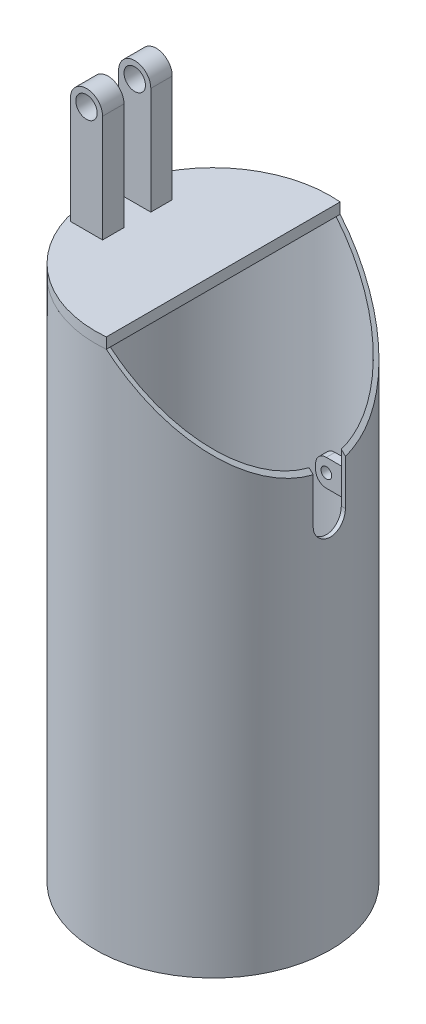
SolidWorks part; units mm, degrees
ref_plane "Plano frontal" through (0, 0, 0) normal (0, 0, 1) x (1, 0, 0)
ref_plane "Plano superior" through (0, 0, 0) normal (0, 1, 0) x (1, 0, 0)
ref_plane "Plano direito" through (0, 0, 0) normal (1, 0, 0) x (0, 0, -1)
sketch "Esboço1" plane through (0, 0, 0) normal (0, 0, 1) x (1, 0, 0)
  line L0 (0, 0) -> (0, 490) construction
  line L1 (0, 0) -> (215.8131, 0) construction
  line L2 (105.78, 490) -> (109.54, 490)
  line L4 (105.78, 0) -> (109.54, 0)
  line L7 (105.78, 0) -> (105.78, 490)
  line L11 (109.54, 490) -> (109.54, 0)
  dimension "D1" = 3.76
  dimension "D6" = 490
  dimension "D7" = 219.08
revolve "Revolução1" add sketch "Esboço1" angle 360 about L0
sketch "Esboço2" plane through (0, 0, 0) normal (0, 0, 1) x (1, 0, 0)
  line L0 (9.54, 490) -> (109.54, 390)
  line L1 (109.54, 490) -> (-109.54, 490) construction
  line L2 (109.54, 0) -> (109.54, 490) construction
  line L3 (109.54, 390) -> (109.54, 490)
  line L4 (109.54, 490) -> (9.54, 490)
  dimension "D1" = 100
  dimension "D2" = 45
extrude "Corte-extrusão1" cut sketch "Esboço2" against normal through all both and the other way through all
sketch "Esboço3" plane through (0, 490, 0) normal (0, 1, 0) x (1, 0, 0)
  line L0 (9.54, 109.1238) -> (9.54, -109.1238)
  arc A0 (9.54, 109.1238) -> (9.54, -109.1238) centre (0, 0) ccw construction
  arc A1 (9.54, 109.1238) -> (9.54, -109.1238) centre (0, 0) ccw
extrude "Ressalto-extrusão1" add sketch "Esboço3" along normal blind 10 separate body
sketch "Esboço4" plane through (0, 0, 0) normal (0, 0, 1) x (1, 0, 0)
  line L0 (-85.54, 500) -> (-85.54, 561.5238) construction
  line L1 (9.54, 500) -> (-109.54, 500) construction
  line L2 (-100.54, 500) -> (-100.54, 600)
  line L3 (-100.54, 500) -> (-70.54, 500)
  line L4 (-70.54, 500) -> (-70.54, 600)
  arc A0 (-70.54, 600) -> (-100.54, 600) centre (-85.54, 600) ccw
  circle A1 centre (-85.54, 600) radius 10
  dimension "D1" = 20
  dimension "D2" = 100
  dimension "D3" = 30
  dimension "D4" = 24
extrude "Ressalto-extrusão2" add sketch "Esboço4" along normal blind 20 from offset 12.5
mirror "Espelhar1" about plane through (0, 0, 0) normal (0, 0, 1) of "Ressalto-extrusão2"
sketch "Esboço5" plane through (0, 0, 0) normal (0, 0, 1) x (1, 0, 0)
  line L0 (105.78, 376.26) -> (85.78, 376.26)
  line L1 (105.78, 0) -> (105.78, 393.76) construction
  line L2 (75.78, 366.26) -> (75.78, 361.26)
  line L3 (85.78, 351.26) -> (105.78, 351.26)
  line L4 (105.78, 351.26) -> (105.78, 376.26)
  circle A0 centre (85.78, 363.76) radius 5
  arc A1 (75.78, 361.26) -> (85.78, 351.26) centre (85.78, 361.26) ccw
  arc A2 (85.78, 376.26) -> (75.78, 366.26) centre (85.78, 366.26) ccw
  point P8 (75.78, 363.76)
  point P11 (75.78, 351.26)
  point P14 (75.78, 376.26)
  dimension "D4" = 10
  dimension "D5" = 10
  dimension "D1" = 30
  dimension "D2" = 25
  dimension "D3" = 20
  dimension "D6" = 30
extrude "Ressalto-extrusão3" add sketch "Esboço5" along normal blind 8 from offset 20
mirror "Espelhar2" about plane through (0, 0, 0) normal (0, 0, 1) of "Ressalto-extrusão3"
sketch "Esboço6" plane through (0, 0, 0) normal (1, 0, 0) x (0, 0, -1)
  line L0 (0, 348.76) -> (0, 475) construction
  line L1 (-15, 348.76) -> (-15, 475)
  line L2 (15, 348.76) -> (15, 475)
  line L5 (-28, 363.76) -> (28, 363.76) construction
  line L6 (-28, 351.26) -> (-28, 376.26) construction
  line L7 (28, 376.26) -> (28, 351.26) construction
  line L8 (-109.1238, 490) -> (109.1238, 490) construction
  arc A0 (-15, 348.76) -> (15, 348.76) centre (0, 348.76) ccw
  arc A1 (15, 475) -> (-15, 475) centre (0, 475) ccw
  point P3 (0, 411.88)
  dimension "D1" = 30
  dimension "D2" = 15
extrude "Corte-extrusão2" cut sketch "Esboço6" along normal through all
